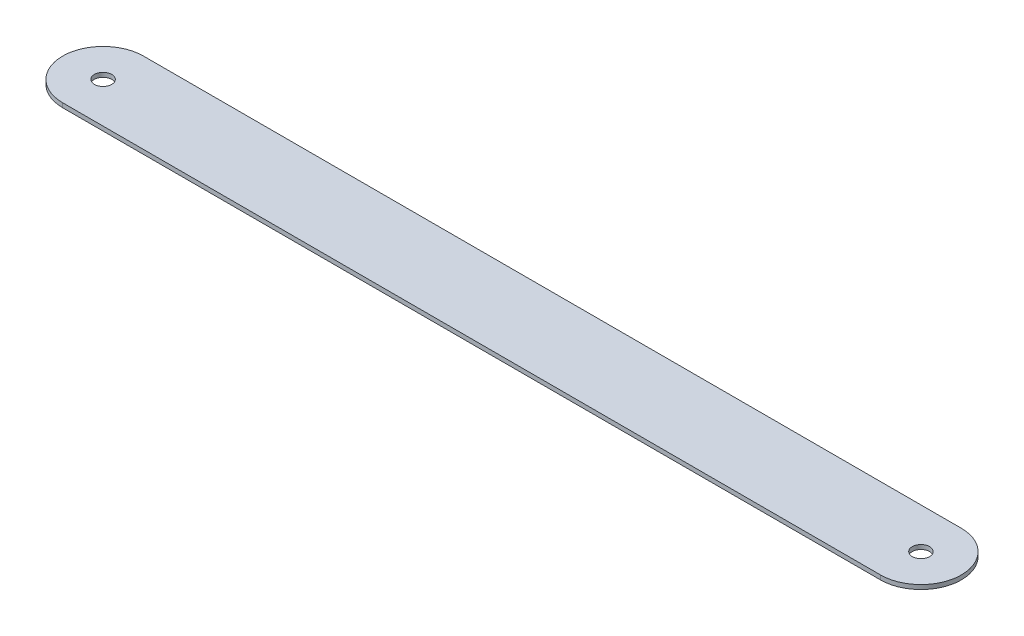
SolidWorks part; units mm, degrees
ref_plane "Front Plane" through (0, 0, 0) normal (0, 0, 1) x (1, 0, 0)
ref_plane "Top Plane" through (0, 0, 0) normal (0, 1, 0) x (1, 0, 0)
ref_plane "Right Plane" through (0, 0, 0) normal (1, 0, 0) x (0, 0, -1)
sketch "Sketch1" plane through (0, 0, 0) normal (0, 1, 0) x (1, 0, 0)
  line L0 (0, 0) -> (283.23, 0) construction
  line L1 (0, 14) -> (283.23, 14)
  line L2 (0, -14) -> (283.23, -14)
  arc A0 (0, 14) -> (0, -14) centre (0, 0) ccw
  arc A1 (283.23, -14) -> (283.23, 14) centre (283.23, 0) ccw
  circle A2 centre (0, 0) radius 3
  circle A3 centre (283.23, 0) radius 3
  point P3 (141.615, 0)
  dimension "D2" = 6
  dimension "D3" = 14
  dimension "D1" = 283.23
extrude "Boss-Extrude1" add sketch "Sketch1" along normal blind 1.5
